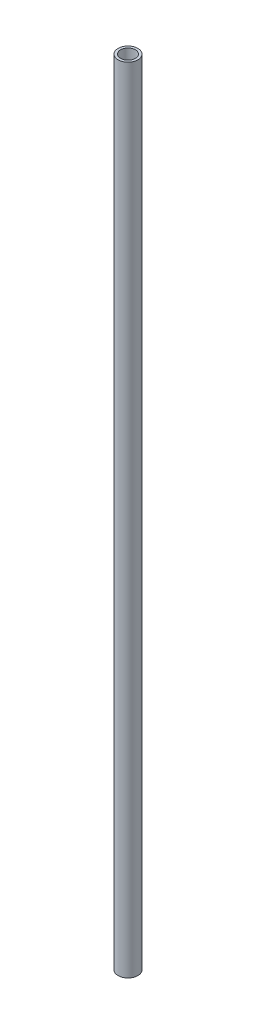
SolidWorks part; units mm, degrees
ref_plane "Front Plane" through (0, 0, 0) normal (0, 0, 1) x (1, 0, 0)
ref_plane "Top Plane" through (0, 0, 0) normal (0, 1, 0) x (1, 0, 0)
ref_plane "Right Plane" through (0, 0, 0) normal (1, 0, 0) x (0, 0, -1)
sketch "Sketch3" plane through (0, 0, 0) normal (0, 1, 0) x (1, 0, 0)
  circle A0 centre (0, 0) radius 12.7
  dimension "D1" = 25.4
extrude "Boss-Extrude1" add sketch "Sketch3" along normal blind 1016
shell "Shell1" thickness 3.175
